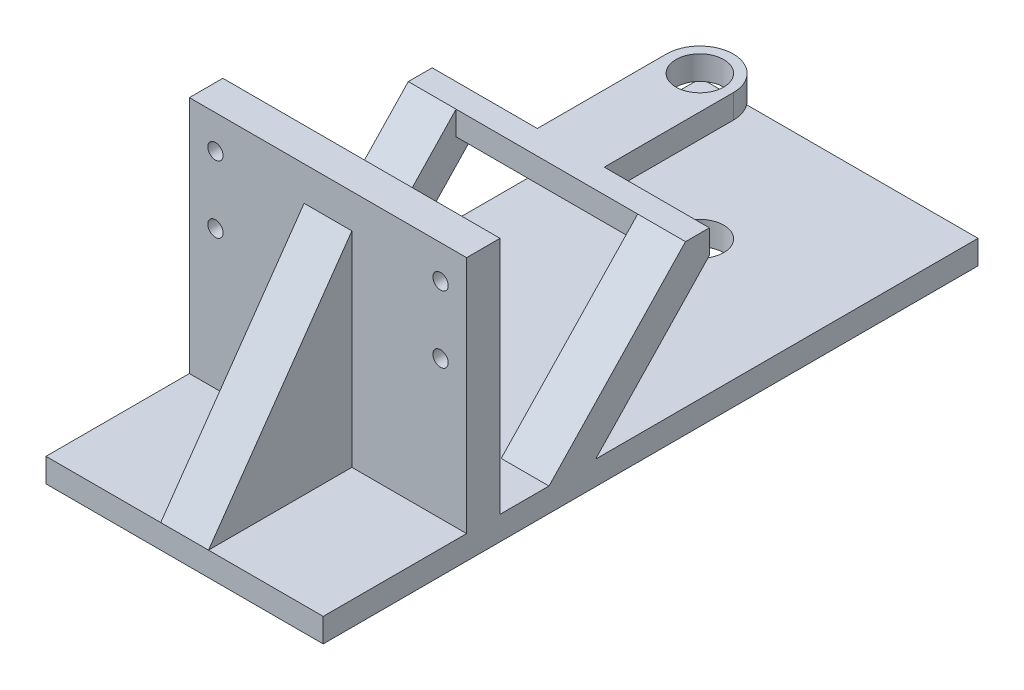
SolidWorks part; units mm, degrees
ref_plane "Front Plane" through (0, 0, 0) normal (0, 0, 1) x (1, 0, 0)
ref_plane "Top Plane" through (0, 0, 0) normal (0, 1, 0) x (1, 0, 0)
ref_plane "Right Plane" through (0, 0, 0) normal (1, 0, 0) x (0, 0, -1)
sketch "Sketch1" plane through (0, 0, 0) normal (0, 0, 1) x (1, 0, 0)
  line L1 (-36.83, 34.925) -> (36.83, 34.925)
  line L2 (-36.83, 34.925) -> (-36.83, -34.925)
  line L3 (-36.83, -34.925) -> (36.83, -34.925)
  line L4 (36.83, 34.925) -> (36.83, -34.925)
  point P4 (0, 34.925)
  point P6 (36.83, 0)
  dimension "D1" = 69.85
  dimension "D2" = 73.66
extrude "Boss-Extrude1" add sketch "Sketch1" along normal blind 8.89
sketch "Sketch2" plane through (0, 0, 0) normal (0, 0, -1) x (-1, 0, 0)
  line L0 (0, 34.925) -> (0, -34.925) construction
  line L1 (-36.83, 34.925) -> (36.83, 34.925) construction
  line L2 (36.83, -34.925) -> (-36.83, -34.925) construction
  circle A0 centre (-29.9085, 26.035) radius 2.032
  circle A1 centre (-29.9085, 8.255) radius 2.032
  circle A2 centre (29.9085, 8.255) radius 2.032
  circle A3 centre (29.9085, 26.035) radius 2.032
  dimension "D1" = 4.064
  dimension "D2" = 4.064
  dimension "D3" = 17.78
  dimension "D4" = 59.817
  dimension "D5" = 8.89
extrude "Cut-Extrude1" cut sketch "Sketch2" against normal up to surface (8.89 mm away) up to face at (0, 0, 8.89)
sketch "Sketch3" plane through (0, 0, 0) normal (0, 0, -1) x (-1, 0, 0)
  line L1 (-36.83, -34.925) -> (36.83, -34.925)
  line L2 (-36.83, -34.925) -> (-36.83, -28.575)
  line L3 (-36.83, -28.575) -> (36.83, -28.575)
  line L4 (36.83, -34.925) -> (36.83, -28.575)
  line L5 (36.83, 34.925) -> (36.83, -34.925) construction
  dimension "D2" = 6.35
extrude "Boss-Extrude2" add sketch "Sketch3" along normal blind 127
sketch "Sketch4" plane through (0, 0, 8.89) normal (0, 0, 1) x (1, 0, 0)
  line L0 (-36.83, 34.925) -> (-36.83, -34.925) construction
  line L1 (36.83, -34.925) -> (-36.83, -34.925)
  line L2 (36.83, -34.925) -> (36.83, -28.575)
  line L3 (36.83, -28.575) -> (-36.83, -28.575)
  line L4 (-36.83, -34.925) -> (-36.83, -28.575)
  dimension "D1" = 6.35
extrude "Boss-Extrude3" add sketch "Sketch4" along normal blind 38.1
sketch "Sketch5" plane through (36.83, 0, 0) normal (1, 0, 0) x (0, 0, -1)
  line L2 (-46.99, -28.575) -> (-8.89, -28.575) construction
  line L3 (-46.99, -28.575) -> (-8.89, 25.8374)
  line L4 (-8.89, -28.575) -> (-8.89, 34.925) construction
  line L6 (-46.99, -28.575) -> (-8.89, -28.575)
  line L7 (-8.89, -28.575) -> (-8.89, 25.8374)
  dimension "D1" = 35
extrude "Boss-Extrude4" add sketch "Sketch5" against normal mid plane 12.7 from offset 36.83 offset against normal yes
sketch "Sketch6" plane through (0, 0, 0) normal (0, 0, -1) x (-1, 0, 0)
  line L0 (0, 34.925) -> (0, -28.575) construction
  line L1 (-36.83, 34.925) -> (36.83, 34.925) construction
  line L2 (36.83, -28.575) -> (-36.83, -28.575) construction
sketch "Sketch7" plane through (0, -28.575, 0) normal (0, 1, 0) x (1, 0, 0)
  line L1 (-36.83, 0) -> (36.83, 0) construction
  circle A0 centre (0, 26.416) radius 2.54
  circle A1 centre (0, 89.916) radius 6.35
  dimension "D1" = 5.08
  dimension "D2" = 12.7
  dimension "D3" = 63.5
  dimension "D4" = 26.416
extrude "Cut-Extrude2" cut sketch "Sketch7" against normal up to surface (6.35 mm away) up to face at (0, -34.925, -40.005)
sketch "Sketch21" plane through (-36.83, 0, 0) normal (-1, 0, 0) x (0, 0, 1)
  line L0 (-25.4, -28.575) -> (-55.626, 3.175)
  line L1 (-127, -28.575) -> (0, -28.575) construction
  line L2 (-55.626, 3.175) -> (-49.276, 3.175)
  line L3 (-49.276, 3.175) -> (-49.276, 9.525)
  line L4 (-49.276, 9.525) -> (-13.0048, -28.575)
  line L6 (-83.566, -28.575) -> (-96.266, -28.575) construction
  line L7 (-25.4, -28.575) -> (-13.0048, -28.575)
  point P10 (-89.916, -28.575)
  dimension "D1" = 31.75
  dimension "D2" = 25.4
  dimension "D3" = 6.35
  dimension "D4" = 6.35
  dimension "D5" = 34.29
extrude "Boss-Extrude15" add sketch "Sketch21" against normal blind 12.7
sketch "Sketch23" plane through (0, 3.175, 0) normal (0, 1, 0) x (1, 0, 0)
  line L0 (-36.83, 49.276) -> (8.89, 49.276)
  line L1 (8.89, 49.276) -> (8.89, 89.916)
  line L2 (-8.89, 89.916) -> (-8.89, 55.626)
  line L3 (-8.89, 55.626) -> (-36.83, 55.626)
  line L4 (-36.83, 127) -> (-36.83, 25.4) construction
  line L5 (-36.83, 49.276) -> (-36.83, 55.626) construction
  line L6 (-36.83, 55.626) -> (-36.83, 49.276)
  arc A0 (8.89, 89.916) -> (-8.89, 89.916) centre (0, 89.916) ccw
  circle A1 centre (0, 89.916) radius 6.35 construction
  circle A2 centre (0, 89.916) radius 6.35
  dimension "D1" = 12.7
  dimension "D2" = 2.54
extrude "Boss-Extrude16" add sketch "Sketch23" along normal blind 6.35
sketch "Sketch24" plane through (36.83, 0, 0) normal (1, 0, 0) x (0, 0, -1)
  line L0 (25.4, -28.575) -> (55.626, 3.175)
  line L1 (55.626, 3.175) -> (49.276, 3.175)
  line L2 (49.276, 3.175) -> (49.276, 9.525)
  line L3 (49.276, 9.525) -> (13.0048, -28.575)
  line L4 (13.0048, -28.575) -> (25.4, -28.575)
extrude "Boss-Extrude17" add sketch "Sketch24" against normal blind 12.7
sketch "Sketch25" plane through (0, 3.175, 0) normal (0, 1, 0) x (1, 0, 0)
  line L1 (36.83, 55.626) -> (8.89, 55.626)
  line L2 (36.83, 55.626) -> (36.83, 49.276)
  line L3 (36.83, 49.276) -> (8.89, 49.276)
  line L4 (8.89, 55.626) -> (8.89, 49.276)
extrude "Boss-Extrude18" add sketch "Sketch25" along normal blind 6.35
